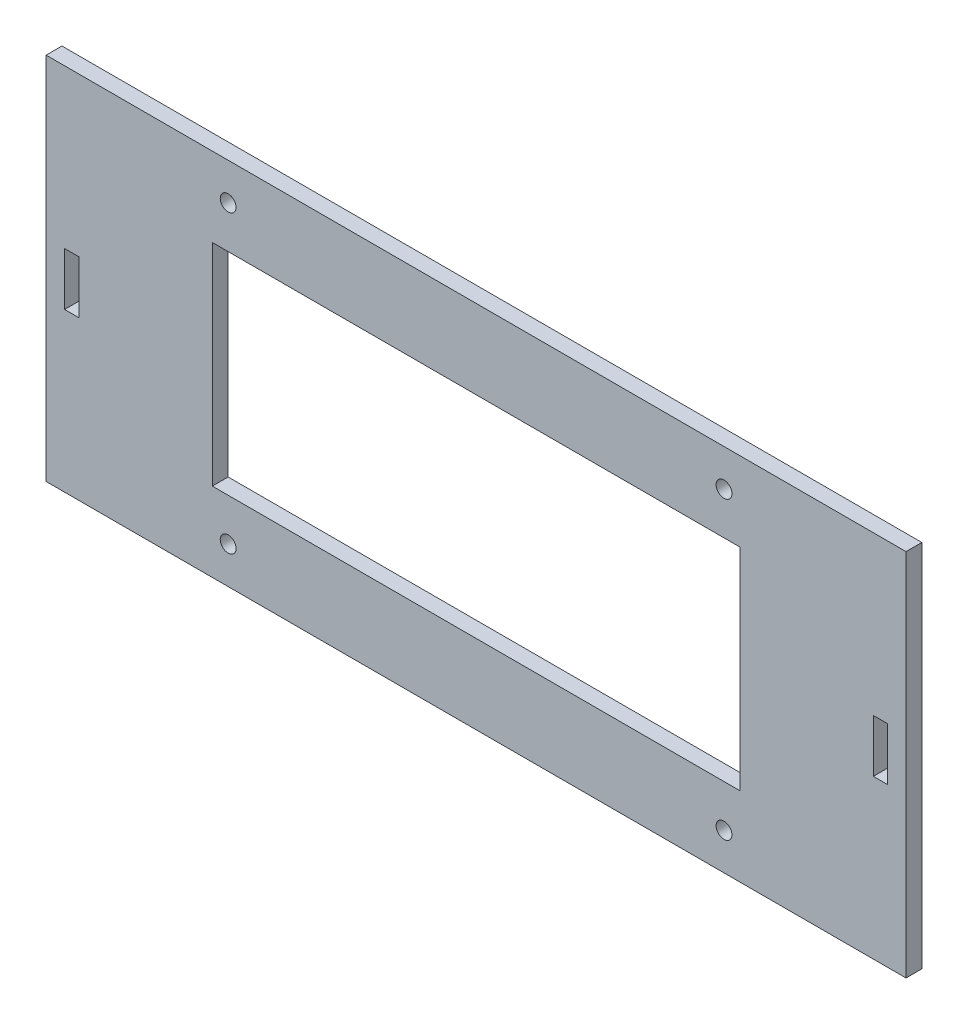
SolidWorks part; units mm, degrees
ref_plane "Front" through (0, 0, 0) normal (0, 0, 1) x (1, 0, 0)
ref_plane "Top" through (0, 0, 0) normal (0, 1, 0) x (1, 0, 0)
ref_plane "Right" through (0, 0, 0) normal (1, 0, 0) x (0, 0, -1)
sketch "Sketch1" plane through (0, 0, 0) normal (0, 0, 1) x (1, 0, 0)
  line L1 (81.5, 35) -> (-81.5, 35)
  line L2 (81.5, 35) -> (81.5, -35)
  line L3 (81.5, -35) -> (-81.5, -35)
  line L4 (-81.5, 35) -> (-81.5, -35)
  line L5 (81.5, 35) -> (-81.5, -35) construction
  line L6 (81.5, -35) -> (-81.5, 35) construction
  point P0 (0, 0)
  dimension "D1" = 70
  dimension "D2" = 163
extrude "Boss-Extrude1" add sketch "Sketch1" along normal blind 3 contours L1 L4 L3 L2
sketch "Sketch2" plane through (0, 0, 3) normal (0, 0, 1) x (1, 0, 0)
  line L0 (-81.5, 35) -> (-81.5, -35) construction
  line L1 (-78, 5) -> (-75.3, 5)
  line L2 (-78, 5) -> (-78, -5)
  line L3 (-78, -5) -> (-75.3, -5)
  line L4 (-75.3, 5) -> (-75.3, -5)
  point P6 (-78, 0)
  point P7 (-81.5, 0)
  dimension "D1" = 10
  dimension "D2" = 3.5
  dimension "D3" = 2.7
extrude "Cut-Extrude1" cut sketch "Sketch2" against normal up to next (3 mm away)
mirror "Mirror1" about plane through (0, 0, 0) normal (1, 0, 0) of "Cut-Extrude1"
sketch "Sketch3" plane through (0, 0, 3) normal (0, 0, 1) x (1, 0, 0)
  line L1 (50, 20) -> (-50, 20)
  line L2 (50, 20) -> (50, -20)
  line L3 (50, -20) -> (-50, -20)
  line L4 (-50, 20) -> (-50, -20)
  line L5 (50, 20) -> (-50, -20) construction
  line L6 (50, -20) -> (-50, 20) construction
  point P0 (0, 0)
  dimension "D1" = 100
  dimension "D2" = 40
extrude "Cut-Extrude2" cut sketch "Sketch3" against normal up to next
sketch "Sketch4" plane through (0, 0, 3) normal (0, 0, 1) x (1, 0, 0)
  line L1 (49, 30) -> (-49, 30) construction
  line L2 (49, 30) -> (49, -30) construction
  line L3 (49, -30) -> (-49, -30) construction
  line L4 (-49, 30) -> (-49, -30) construction
  line L5 (49, 30) -> (-49, -30) construction
  line L6 (49, -30) -> (-49, 30) construction
  circle A0 centre (47, 28) radius 1.5
  point P0 (0, 0)
  dimension "D3" = 3
  dimension "D1" = 98
  dimension "D2" = 60
  dimension "D4" = 4
  dimension "D5" = 4
extrude "Cut-Extrude3" cut sketch "Sketch4" against normal up to next (3 mm away)
mirror "Mirror2" about plane through (0, 0, 0) normal (1, 0, 0) of "Cut-Extrude3"
mirror "Mirror3" about plane through (0, 0, 0) normal (0, 1, 0) of "Mirror2", "Cut-Extrude3"
